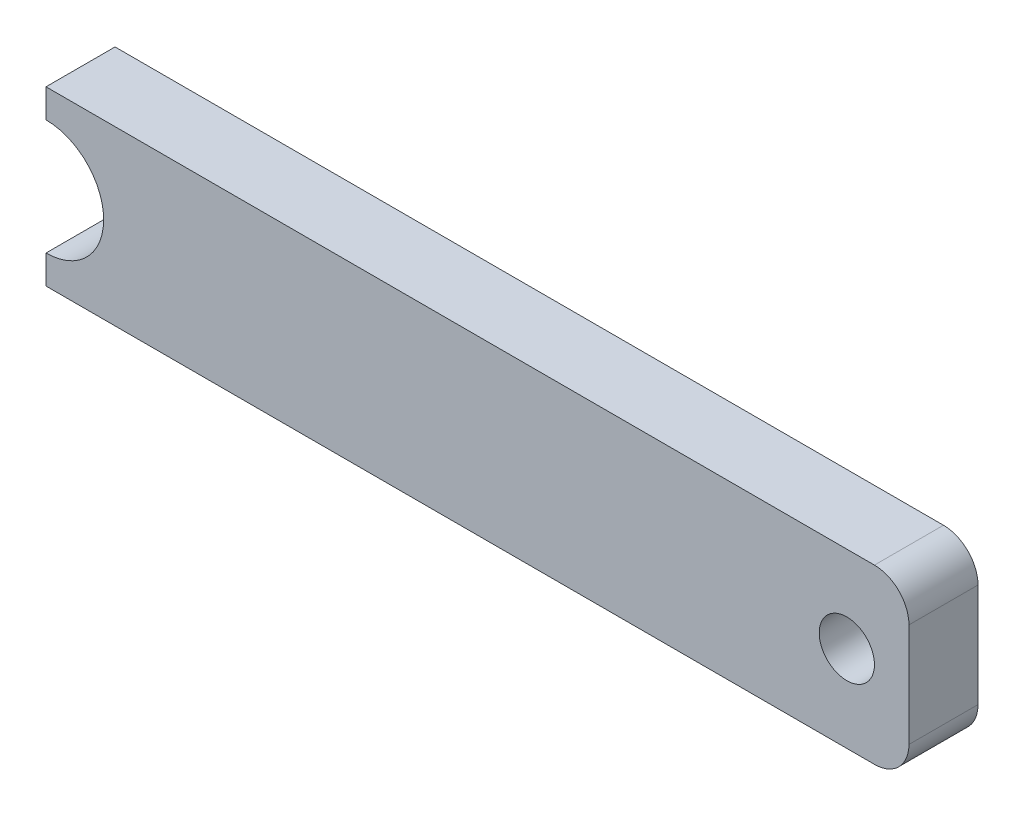
SolidWorks part; units mm, degrees
ref_plane "Front Plane" through (0, 0, 0) normal (0, 0, 1) x (1, 0, 0)
ref_plane "Top Plane" through (0, 0, 0) normal (0, 1, 0) x (1, 0, 0)
ref_plane "Right Plane" through (0, 0, 0) normal (1, 0, 0) x (0, 0, -1)
sketch "Sketch1" plane through (0, 0, 0) normal (0, 0, 1) x (1, 0, 0)
  line L0 (57.5, 7.5) -> (57.5, -7.5) construction
  line L1 (-62.5, 12.5) -> (57.5, 12.5)
  line L2 (-62.5, 12.5) -> (-62.5, 8.35)
  line L3 (-62.5, -12.5) -> (57.5, -12.5)
  line L4 (62.5, 7.5) -> (62.5, -7.5)
  line L5 (-62.5, 12.5) -> (62.5, -12.5) construction
  line L6 (-62.5, -12.5) -> (62.5, 12.5) construction
  line L7 (-62.5, -8.35) -> (-62.5, -12.5)
  arc A0 (62.5, -7.5) -> (57.5, -12.5) centre (57.5, -7.5) cw
  arc A1 (62.5, 7.5) -> (57.5, 12.5) centre (57.5, 7.5) ccw
  circle A2 centre (53.5, 0) radius 4
  arc A3 (-62.5, -8.35) -> (-62.5, 8.35) centre (-62.5, 0) ccw
  point P0 (0, 0)
  point P14 (57.5, 0)
  dimension "D3" = 5
  dimension "D1" = 25
  dimension "D2" = 125
extrude "Boss-Extrude1" add sketch "Sketch1" along normal blind 10
